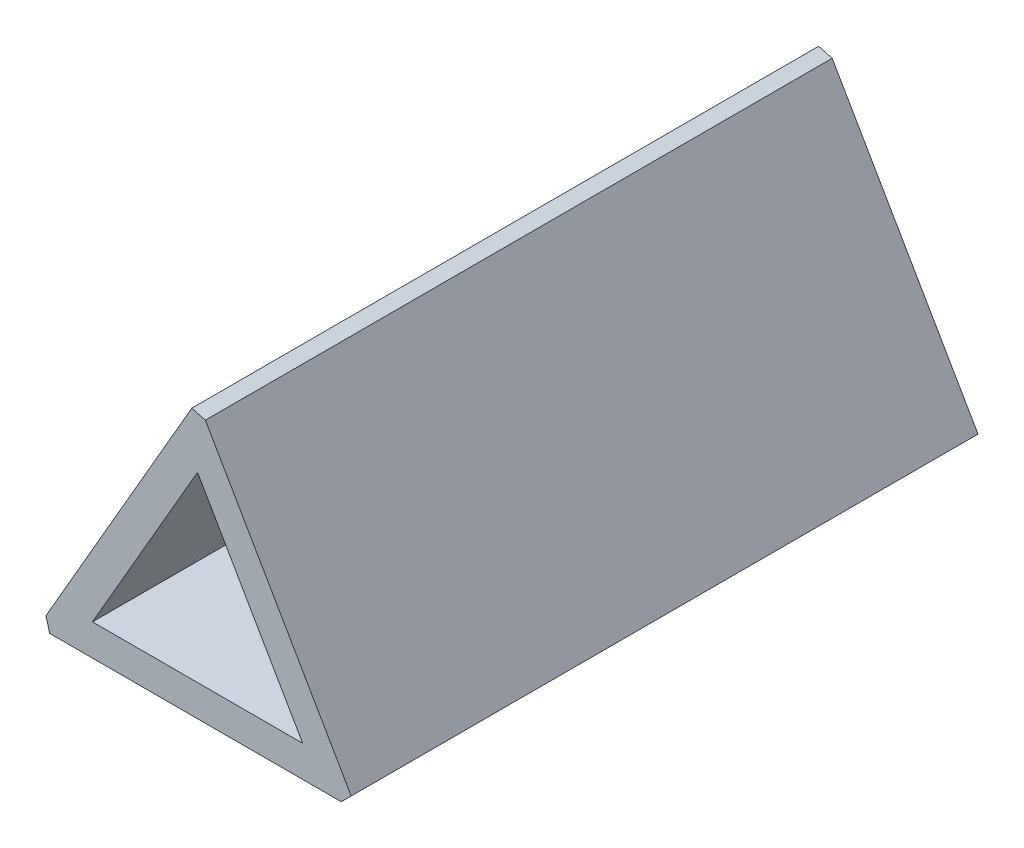
SolidWorks part; units mm, degrees
ref_plane "Front Plane" through (0, 0, 0) normal (0, 0, 1) x (1, 0, 0)
ref_plane "Top Plane" through (0, 0, 0) normal (0, 1, 0) x (1, 0, 0)
ref_plane "Right Plane" through (0, 0, 0) normal (1, 0, 0) x (0, 0, -1)
sketch "Sketch1" plane through (0, 0, 0) normal (0, 0, 1) x (1, 0, 0)
  line L0 (0, 7.7451) -> (-6.7074, -3.8725)
  line L1 (-6.7074, -3.8725) -> (6.7074, -3.8725)
  line L2 (6.7074, -3.8725) -> (0, 7.7451)
  line L4 (0, 11.7451) -> (-10.1715, -5.8725)
  line L5 (-10.1715, -5.8725) -> (10.1715, -5.8725)
  line L6 (10.1715, -5.8725) -> (0, 11.7451)
  circle A1 centre (0, 0) radius 5.8725 construction
  dimension "D1" = 20.3431
  dimension "D2" = 2
extrude "Boss-Extrude1" add sketch "Sketch1" along normal blind 40
chamfer "Chamfer1" distance 1 angle 45 3 edges at (-10.1715, -5.8725, 20) (10.1715, -5.8725, 20) (0, 11.7451, 20)
